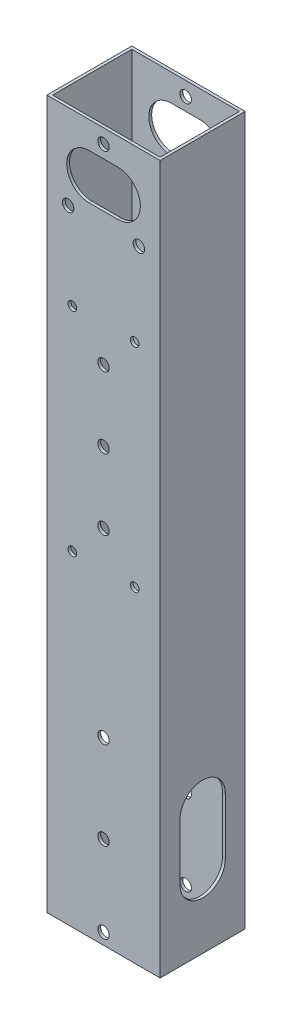
SolidWorks part; units mm, degrees
material "6063-T5"
ref_plane "前视基准面" through (0, 0, 0) normal (0, 0, 1) x (1, 0, 0)
ref_plane "上视基准面" through (0, 0, 0) normal (0, 1, 0) x (1, 0, 0)
ref_plane "右视基准面" through (0, 0, 0) normal (1, 0, 0) x (0, 0, -1)
other "Configuration Table"
sketch "草图1" plane through (0, 0, 0) normal (0, 1, 0) x (1, 0, 0)
  line L1 (-20, -15) -> (20, -15)
  line L2 (-20, -15) -> (-20, 15)
  line L3 (-20, 15) -> (20, 15)
  line L4 (20, -15) -> (20, 15)
  line L5 (-20, -15) -> (20, 15) construction
  line L6 (-20, 15) -> (20, -15) construction
  point P0 (0, 0)
  dimension "D1" = 40
  dimension "D2" = 30
extrude "凸台-拉伸1" add sketch "草图1" along normal mid plane 250
sketch "草图2" plane through (0, 0, 0) normal (0, 1, 0) x (1, 0, 0)
  line L8 (19, -14) -> (19, 14)
  line L9 (19, 14) -> (-19, 14)
  line L10 (-19, 14) -> (-19, -14)
  line L11 (-19, -14) -> (19, -14)
  line L12 (19, -14) -> (19, 14)
  line L13 (19, 14) -> (-19, 14)
  line L14 (-19, 14) -> (-19, -14)
  line L15 (-19, -14) -> (19, -14)
  dimension "D1" = 1
extrude "切除-拉伸1" cut sketch "草图2" against normal through all both and the other way through all
sketch "草图3" plane through (0, 0, 15) normal (0, 0, 1) x (1, 0, 0)
  circle A0 centre (0, -61.5) radius 2.025
  circle A1 centre (0, -92.5) radius 2.025
  circle A2 centre (0, -121) radius 2.025
  dimension "D1" = 4.05
extrude "切除-拉伸2" cut sketch "草图3" against normal through all both
sketch "草图4" plane through (0, 0, -15) normal (0, 0, -1) x (-1, 0, 0)
  line L0 (20, 125) -> (20, -125) construction
  line L1 (-20, 125) -> (-20, -125) construction
  line L2 (-20, 125) -> (20, 125) construction
  line L7 (-20, -125) -> (20, -125)
  line L8 (20, -125) -> (20, 125)
  line L9 (20, 125) -> (-20, 125)
  line L10 (-20, 125) -> (-20, -125)
  line L11 (-20, -125) -> (20, -125)
  circle A0 centre (0, 120) radius 2.025
  circle A1 centre (12.5, 95) radius 2.025
  circle A2 centre (-12.5, 95) radius 2.025
  dimension "D1" = 4.05
  dimension "D2" = 25
  dimension "D3" = 25
  dimension "D4" = 7.5
  dimension "D5" = 7.5
  dimension "D6" = 5
  dimension "D8" = 20
  dimension "D7" = 0
extrude "切除-拉伸3" cut sketch "草图4" against normal through all both contours A0 | A2 | A1
sketch "草图5" plane through (0, 0, -15) normal (0, 0, -1) x (-1, 0, 0)
  line L0 (-20, -125) -> (20, -125) construction
  line L1 (-11, -10) -> (11, -10) construction
  line L2 (-11, -10) -> (-11, 65) construction
  line L3 (-11, 65) -> (11, 65) construction
  line L4 (11, -10) -> (11, 65) construction
  line L5 (-11, -10) -> (11, 65) construction
  line L6 (-11, 65) -> (11, -10) construction
  circle A0 centre (-11, 65) radius 1.525
  circle A1 centre (11, 65) radius 1.525
  circle A2 centre (-11, -10) radius 1.525
  circle A3 centre (11, -10) radius 1.525
  point P0 (0, 27.5)
  dimension "D3" = 3.05
  dimension "D1" = 22
  dimension "D2" = 75
  dimension "D4" = 115
extrude "切除-拉伸4" cut sketch "草图5" against normal through all
sketch "草图6" plane through (0, 0, -15) normal (0, 0, -1) x (-1, 0, 0)
  line L0 (-11, 65) -> (11, 65) construction
  line L1 (0, 65) -> (0, -10) construction
  line L2 (0, -10) -> (11, -10) construction
  line L3 (0, 27.5) -> (20, 27.5) construction
  line L4 (20, 125) -> (20, -125) construction
  circle A0 centre (0, 27.5) radius 2.025
  circle A1 centre (0, 52.5) radius 2.025
  circle A2 centre (0, 2.5) radius 2.025
  dimension "D1" = 4.05
  dimension "D2" = 50
extrude "切除-拉伸5" cut sketch "草图6" against normal through all
sketch "草图7" plane through (0, 0, -15) normal (0, 0, -1) x (-1, 0, 0)
  line L0 (0, 52.5) -> (0, 2.5) construction
  line L1 (7, 52.5) -> (7, 2.5)
  line L2 (-7, 52.5) -> (-7, 2.5)
  arc A0 (7, 52.5) -> (-7, 52.5) centre (0, 52.5) ccw
  arc A1 (-7, 2.5) -> (7, 2.5) centre (0, 2.5) ccw
  point P4 (0, 27.5)
  dimension "D1" = 7
extrude "切除-拉伸6" cut sketch "草图7" against normal blind 10
sketch "草图8" plane through (0, 0, -15) normal (0, 0, -1) x (-1, 0, 0)
  circle A0 centre (11, 65) radius 3.25
  circle A1 centre (-11, 65) radius 3.25
  circle A2 centre (11, -10) radius 3.25
  circle A3 centre (-11, -10) radius 3.25
  dimension "D1" = 6.5
extrude "切除-拉伸7" cut sketch "草图8" against normal blind 10
sketch "草图9" plane through (20, 0, 0) normal (1, 0, 0) x (0, 0, -1)
  line L0 (0, -100) -> (0, -80) construction
  line L1 (-8, -100) -> (-8, -80)
  line L2 (8, -100) -> (8, -80)
  line L3 (0, -80) -> (0, 0) construction
  line L4 (-15, -125) -> (15, -125) construction
  arc A0 (-8, -100) -> (8, -100) centre (0, -100) ccw
  arc A1 (8, -80) -> (-8, -80) centre (0, -80) ccw
  point P3 (0, -90)
  dimension "D1" = 8
  dimension "D2" = 20
  dimension "D3" = 35
extrude "切除-拉伸8" cut sketch "草图9" against normal through all both and the other way through all
sketch "草图10" plane through (0, 0, -15) normal (0, 0, -1) x (-1, 0, 0)
  line L0 (-5, 107.5) -> (5, 107.5) construction
  line L1 (-5, 115.5) -> (5, 115.5)
  line L2 (-5, 99.5) -> (5, 99.5)
  line L3 (20, 125) -> (20, -125) construction
  arc A0 (-5, 115.5) -> (-5, 99.5) centre (-5, 107.5) ccw
  arc A1 (5, 99.5) -> (5, 115.5) centre (5, 107.5) ccw
  circle A2 centre (-11, 65) radius 3.25 construction
  point P2 (0, 107.5)
  point P7 (0, 107.5)
  dimension "D1" = 8
  dimension "D2" = 10
  dimension "D3" = 20
  dimension "D4" = 42.5
extrude "切除-拉伸9" cut sketch "草图10" against normal through all both and the other way through all
